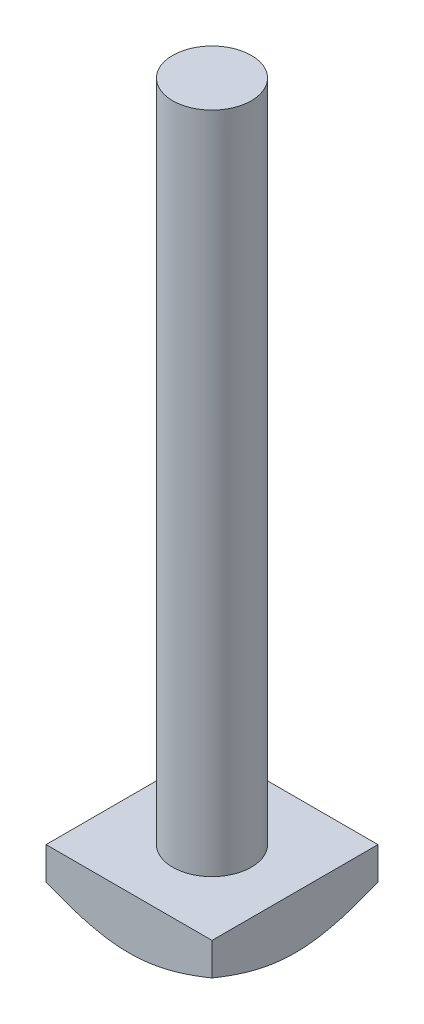
SolidWorks part; units mm, degrees
ref_plane "Front Plane" through (0, 0, 0) normal (0, 0, 1) x (1, 0, 0)
ref_plane "Top Plane" through (0, 0, 0) normal (0, 1, 0) x (1, 0, 0)
ref_plane "Right Plane" through (0, 0, 0) normal (1, 0, 0) x (0, 0, -1)
sketch "Sketch1" plane through (0, 0, 0) normal (0, 1, 0) x (1, 0, 0)
  line L1 (0, 0) -> (19, 0)
  line L2 (0, 0) -> (0, 19)
  line L3 (0, 19) -> (19, 19)
  line L4 (19, 0) -> (19, 19)
  dimension "D1" = 19
  dimension "D2" = 19
  dimension "D3" = 19
  dimension "D4" = 19
extrude "Boss-Extrude1" add sketch "Sketch1" along normal blind 6
sketch "Sketch2" plane through (0, 6, 0) normal (0, 1, 0) x (1, 0, 0)
  line L1 (0, 0) -> (19, 0) construction
  circle A0 centre (9.5, 9.5) radius 4.5
  dimension "D1" = 9
  dimension "D2" = 9.5
  dimension "D3" = 9.5
extrude "Boss-Extrude2" add sketch "Sketch2" along normal blind 76
sketch "Sketch13" plane through (0, 0, 0) normal (0, -1, 0) x (-1, 0, 0)
  line L0 (-19, 0) -> (-19, 19) construction
  line L3 (0, 0) -> (-19, 0) construction
  circle A0 centre (-9.5, 9.5) radius 9.5
  point P6 (-12.7721, 0)
  point P7 (-8.9155, 0)
  dimension "D3" = 19
  dimension "D1" = 9.5
  dimension "D2" = 9.5
extrude "Cut-Extrude1" cut sketch "Sketch13" against normal blind 6 draft 60 flip side to cut contours A0
